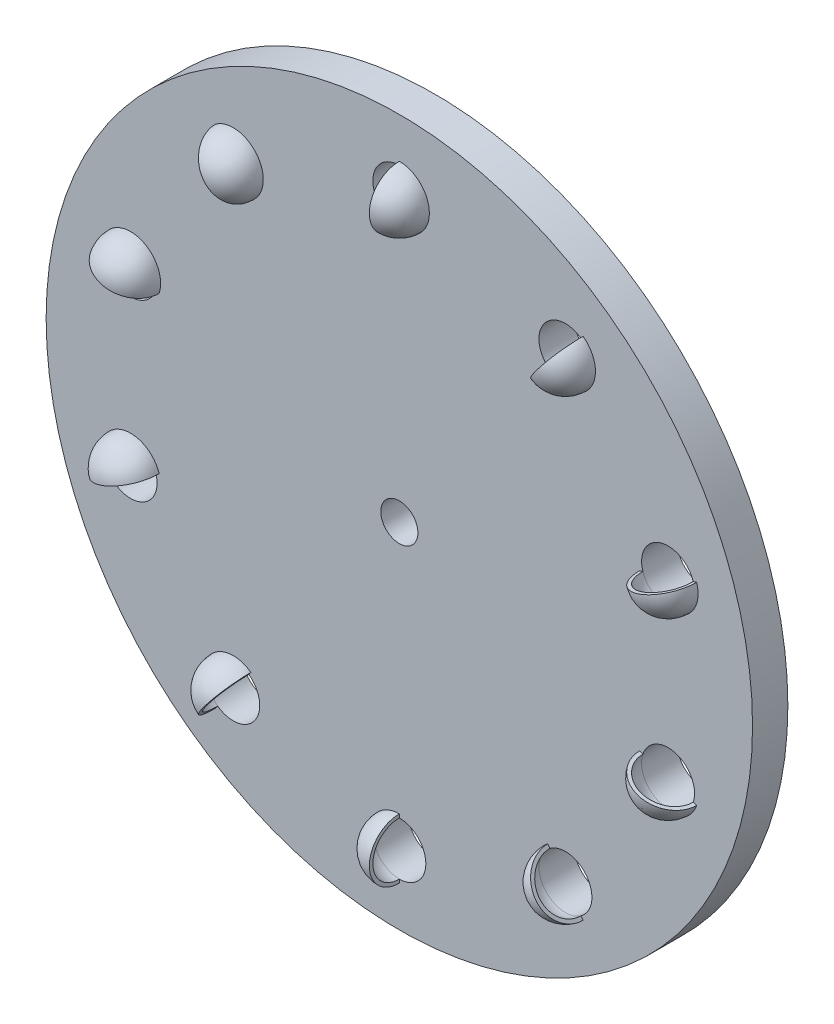
SolidWorks part; units mm, degrees
ref_plane "Front Plane" through (0, 0, 0) normal (0, 0, 1) x (1, 0, 0)
ref_plane "Top Plane" through (0, 0, 0) normal (0, 1, 0) x (1, 0, 0)
ref_plane "Right Plane" through (0, 0, 0) normal (1, 0, 0) x (0, 0, -1)
sketch "Sketch2" plane through (0, 0, 0) normal (0, 0, 1) x (1, 0, 0)
  line L0 (0, 0) -> (0, 122.0736) construction
  circle A0 centre (0, 0) radius 100
  circle A21 centre (0, 0) radius 5.25
  circle A22 centre (0, 80) radius 7.5
  circle A23 centre (47.0228, 64.7214) radius 7.5
  circle A24 centre (76.0845, 24.7214) radius 7.5
  circle A25 centre (76.0845, -24.7214) radius 7.5
  circle A26 centre (47.0228, -64.7214) radius 7.5
  circle A27 centre (0, -80) radius 7.5
  circle A28 centre (-47.0228, -64.7214) radius 7.5
  circle A29 centre (-76.0845, -24.7214) radius 7.5
  circle A30 centre (-76.0845, 24.7214) radius 7.5
  circle A31 centre (-47.0228, 64.7214) radius 7.5
  point P25 (0, 0)
  point P26 (0, 0)
  point P29 (0, 0)
  dimension "D1" = 200
  dimension "D3" = 15
  dimension "D2" = 80
  dimension "D4" = 10.5
  dimension "D5" = 10
extrude "Boss-Extrude1" add sketch "Sketch2" along normal blind 10
sketch "Sketch7" plane through (0, 0, 10) normal (0, 0, 1) x (1, 0, 0)
  line L0 (0, -88.5) -> (0, -87.5)
  line L1 (0, -72.5) -> (0, -71.5)
  arc A2 (0, -72.5) -> (0, -87.5) centre (0, -80) ccw
  arc A3 (0, -88.5) -> (0, -71.5) centre (0, -80) cw
revolve "Revolve6" add sketch "Sketch7" angle 90 about L0
pattern_circular "CirPattern3" count 10 over 360 about axis through (0, 0, 0) along (0, 0, 1) of "Revolve6"
